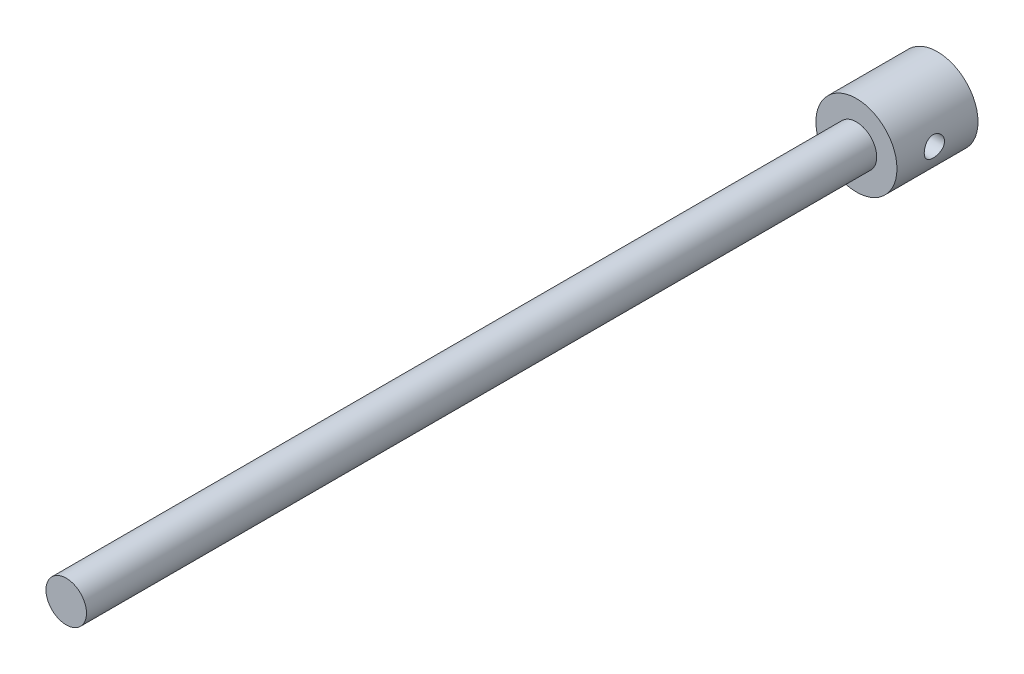
SolidWorks part; units mm, degrees
material "Plain Carbon Steel"
ref_plane "Front" through (0, 0, 0) normal (0, 0, 1) x (1, 0, 0)
ref_plane "Top" through (0, 0, 0) normal (0, 1, 0) x (1, 0, 0)
ref_plane "Right" through (0, 0, 0) normal (1, 0, 0) x (0, 0, -1)
sketch "Sketch1" plane through (0, 0, 0) normal (0, 0, 1) x (1, 0, 0)
  circle A0 centre (0, 0) radius 25.4
  dimension "D1" = 50.8
extrude "Extrude1" add sketch "Sketch1" along normal blind 50.8
sketch "Sketch2" plane through (0, 0, 50.8) normal (0, 0, 1) x (1, 0, 0)
  circle A0 centre (0, 0) radius 12.7
  dimension "D1" = 25.4
extrude "Extrude2" add sketch "Sketch2" along normal blind 495.3
cosmetic thread "Cosmetic Thread1" parameters "D2"=23.02
cosmetic thread "Cosmetic Thread2" parameters "D2"=23.02
cosmetic thread "Cosmetic Thread3" parameters "D2"=23.02
sketch "Sketch3" plane through (0, 0, 0) normal (1, 0, 0) x (0, 0, -1)
  circle A0 centre (-27.3473, 0) radius 6.35
  dimension "D1" = 12.7
extrude "Cut-Extrude1" cut sketch "Sketch3" against normal through all and the other way through all
